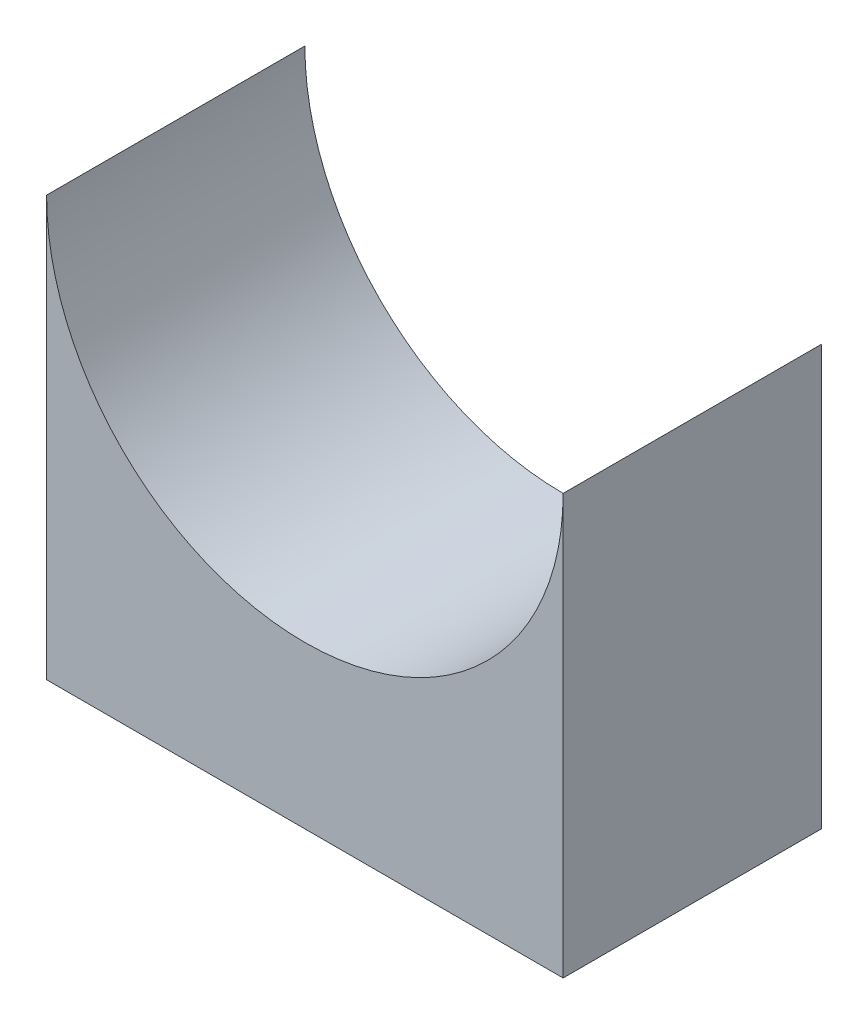
SolidWorks part; units mm, degrees
ref_plane "Front Plane" through (0, 0, 0) normal (0, 0, 1) x (1, 0, 0)
ref_plane "Top Plane" through (0, 0, 0) normal (0, 1, 0) x (1, 0, 0)
ref_plane "Right Plane" through (0, 0, 0) normal (1, 0, 0) x (0, 0, -1)
sketch "Sketch1" plane through (0, 0, 0) normal (0, 0, 1) x (1, 0, 0)
  line L0 (0, 0) -> (40, 0)
  line L1 (40, 0) -> (40, 32.5)
  line L2 (0, 0) -> (0, 32.5)
  arc A0 (40, 32.5) -> (0, 32.5) centre (20, 32.5) cw
  dimension "D1" = 40
  dimension "D2" = 32.5
  dimension "D3" = 32.5
extrude "Boss-Extrude1" add sketch "Sketch1" along normal blind 20
